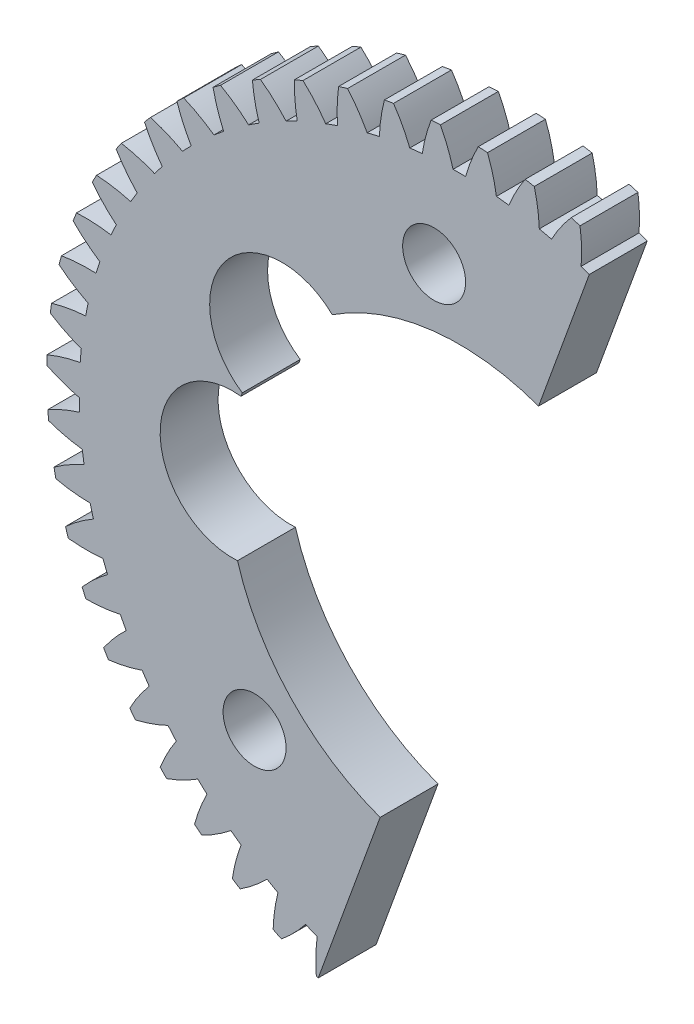
SolidWorks part; units mm, degrees
ref_plane "Front Plane" through (0, 0, 0) normal (0, 0, 1) x (1, 0, 0)
ref_plane "Top Plane" through (0, 0, 0) normal (0, 1, 0) x (1, 0, 0)
ref_plane "Right Plane" through (0, 0, 0) normal (1, 0, 0) x (0, 0, -1)
sketch "Model" plane through (0, 0, 0) normal (0, 0, 1) x (1, 0, 0)
  circle A0 centre (0, 0) radius 2.5
  arc A1 (-28.4774, 1.1339) -> (-28.4957, 0.4937) centre (0, 0) ccw
  arc A2 (-26.1862, 1.814) -> (-28.4774, 1.1339) centre (-24.2203, -9.0089) ccw
  arc A3 (-26.112, 2.6779) -> (-26.1862, 1.814) centre (0, 0) ccw
  arc A4 (-28.2537, 3.7387) -> (-26.112, 2.6779) centre (-22.3294, 13.0071) ccw
  arc A5 (-28.1626, 4.3727) -> (-28.2537, 3.7387) centre (0, 0) ccw
  arc A6 (-25.8088, 4.7871) -> (-28.1626, 4.3727) centre (-25.0894, -6.1893) ccw
  arc A7 (-25.6366, 5.637) -> (-25.8088, 4.7871) centre (0, 0) ccw
  arc A8 (-27.6434, 6.9351) -> (-25.6366, 5.637) centre (-20.7011, 15.4677) ccw
  arc A9 (-27.4805, 7.5545) -> (-27.6434, 6.9351) centre (0, 0) ccw
  arc A10 (-25.0949, 7.6979) -> (-27.4805, 7.5545) centre (-25.6314, -3.289) ccw
  arc A11 (-24.8269, 8.5226) -> (-25.0949, 7.6979) centre (0, 0) ccw
  arc A12 (-26.6726, 10.041) -> (-24.8269, 8.5226) centre (-18.803, 17.7266) ccw
  arc A13 (-26.4403, 10.6378) -> (-26.6726, 10.041) centre (0, 0) ccw
  arc A14 (-24.0538, 10.5083) -> (-26.4403, 10.6378) centre (-25.8392, -0.3458) ccw
  arc A15 (-23.6936, 11.2971) -> (-24.0538, 10.5083) centre (0, 0) ccw
  arc A16 (-25.3542, 13.016) -> (-23.6936, 11.2971) centre (-16.6598, 19.7544) ccw
  arc A17 (-25.0553, 13.5824) -> (-25.3542, 13.016) centre (0, 0) ccw
  arc A18 (-22.6991, 13.1818) -> (-25.0553, 13.5824) centre (-25.7102, 2.6019) ccw
  arc A19 (-22.2513, 13.9244) -> (-22.6991, 13.1818) centre (0, 0) ccw
  arc A20 (-23.7052, 15.8213) -> (-22.2513, 13.9244) centre (-14.2993, 21.5247) ccw
  arc A21 (-23.3437, 16.35) -> (-23.7052, 15.8213) centre (0, 0) ccw
  arc A22 (-21.0486, 15.6834) -> (-23.3437, 16.35) centre (-25.246, 5.5157) ccw
  arc A23 (-20.519, 16.3701) -> (-21.0486, 15.6834) centre (0, 0) ccw
  arc A24 (-21.7472, 18.4203) -> (-20.519, 16.3701) centre (-11.7525, 23.0144) ccw
  arc A25 (-21.3278, 18.9044) -> (-21.7472, 18.4203) centre (0, 0) ccw
  arc A26 (-19.1236, 17.9805) -> (-21.3278, 18.9044) centre (-24.4527, 8.3576) ccw
  arc A27 (-18.5192, 18.6024) -> (-19.1236, 17.9805) centre (0, 0) ccw
  arc A28 (-19.5057, 20.7793) -> (-18.5192, 18.6024) centre (-9.0524, 24.2041) ccw
  arc A29 (-19.0338, 21.2123) -> (-19.5057, 20.7793) centre (0, 0) ccw
  arc A30 (-16.9493, 20.0432) -> (-19.0338, 21.2123) centre (-23.3407, 11.0905) ccw
  arc A31 (-16.278, 20.5921) -> (-16.9493, 20.0432) centre (0, 0) ccw
  arc A32 (-17.0099, 22.8673) -> (-16.278, 20.5921) centre (-6.2344, 25.0782) ccw
  arc A33 (-16.4918, 23.2438) -> (-17.0099, 22.8673) centre (0, 0) ccw
  arc A34 (-14.5541, 21.8446) -> (-16.4918, 23.2438) centre (-21.9243, 13.6788) ccw
  arc A35 (-13.8246, 22.3135) -> (-14.5541, 21.8446) centre (0, 0) ccw
  arc A36 (-14.2923, 24.6572) -> (-13.8246, 22.3135) centre (-3.335, 25.6254) ccw
  arc A37 (-13.7347, 24.9722) -> (-14.2923, 24.6572) centre (0, 0) ccw
  arc A38 (-11.9691, 23.3613) -> (-13.7347, 24.9722) centre (-20.2221, 16.0889) ccw
  arc A39 (-11.1909, 23.7439) -> (-11.9691, 23.3613) centre (0, 0) ccw
  arc A40 (-11.3885, 26.1257) -> (-11.1909, 23.7439) centre (-0.3922, 25.8386) ccw
  arc A41 (-10.7985, 26.375) -> (-11.3885, 26.1257) centre (0, 0) ccw
  arc A42 (-9.2281, 24.5734) -> (-10.7985, 26.375) centre (-18.2563, 18.2891) ccw
  arc A43 (-8.4114, 24.8648) -> (-9.2281, 24.5734) centre (0, 0) ccw
  arc A44 (-8.3361, 27.2536) -> (-8.4114, 24.8648) centre (2.5557, 25.7149) ccw
  arc A45 (-7.7216, 27.434) -> (-8.3361, 27.2536) centre (0, 0) ccw
  arc A46 (-6.3668, 25.4651) -> (-7.7216, 27.434) centre (-16.0525, 20.251) ccw
  arc A47 (-5.5222, 25.6616) -> (-6.3668, 25.4651) centre (0, 0) ccw
  arc A48 (-5.1751, 28.0262) -> (-5.5222, 25.6616) centre (5.4703, 25.2559) ccw
  arc A49 (-4.544, 28.1354) -> (-5.1751, 28.0262) centre (0, 0) ccw
  arc A50 (-3.4225, 26.0249) -> (-4.544, 28.1354) centre (-13.6394, 21.9488) ccw
  arc A51 (-2.561, 26.1238) -> (-3.4225, 26.0249) centre (0, 0) ccw
  arc A52 (-1.9466, 28.4334) -> (-2.561, 26.1238) centre (8.3136, 24.4677) ccw
  arc A53 (-1.3072, 28.47) -> (-1.9466, 28.4334) centre (0, 0) ccw
  arc A54 (-0.4336, 26.2454) -> (-1.3072, 28.47) centre (-11.0486, 23.3605) ccw
  arc A55 (0.4336, 26.2454) -> (-0.4336, 26.2454) centre (0, 0) ccw
  arc A56 (1.3072, 28.47) -> (0.4336, 26.2454) centre (11.0486, 23.3605) ccw
  arc A57 (1.9466, 28.4334) -> (1.3072, 28.47) centre (0, 0) ccw
  arc A58 (2.561, 26.1238) -> (1.9466, 28.4334) centre (-8.3136, 24.4677) ccw
  arc A59 (3.4225, 26.0249) -> (2.561, 26.1238) centre (0, 0) ccw
  arc A60 (4.544, 28.1354) -> (3.4225, 26.0249) centre (13.6394, 21.9488) ccw
  arc A61 (5.1751, 28.0262) -> (4.544, 28.1354) centre (0, 0) ccw
  arc A62 (5.5222, 25.6616) -> (5.1751, 28.0262) centre (-5.4703, 25.2559) ccw
  arc A63 (6.3668, 25.4651) -> (5.5222, 25.6616) centre (0, 0) ccw
  arc A64 (7.7216, 27.434) -> (6.3668, 25.4651) centre (16.0525, 20.251) ccw
  arc A65 (8.3361, 27.2536) -> (7.7216, 27.434) centre (0, 0) ccw
  arc A66 (8.4114, 24.8648) -> (8.3361, 27.2536) centre (-2.5557, 25.7149) ccw
  arc A67 (9.2281, 24.5734) -> (8.4114, 24.8648) centre (0, 0) ccw
  arc A68 (10.7985, 26.375) -> (9.2281, 24.5734) centre (18.2563, 18.2891) ccw
  arc A69 (11.3885, 26.1257) -> (10.7985, 26.375) centre (0, 0) ccw
  arc A70 (11.1909, 23.7439) -> (11.3885, 26.1257) centre (0.3922, 25.8386) ccw
  arc A71 (11.9691, 23.3613) -> (11.1909, 23.7439) centre (0, 0) ccw
  arc A72 (13.7347, 24.9722) -> (11.9691, 23.3613) centre (20.2221, 16.0889) ccw
  arc A73 (14.2923, 24.6572) -> (13.7347, 24.9722) centre (0, 0) ccw
  arc A74 (13.8246, 22.3135) -> (14.2923, 24.6572) centre (3.335, 25.6254) ccw
  arc A75 (14.5541, 21.8446) -> (13.8246, 22.3135) centre (0, 0) ccw
  arc A76 (16.4918, 23.2438) -> (14.5541, 21.8446) centre (21.9243, 13.6788) ccw
  arc A77 (17.0099, 22.8673) -> (16.4918, 23.2438) centre (0, 0) ccw
  arc A78 (16.278, 20.5921) -> (17.0099, 22.8673) centre (6.2344, 25.0782) ccw
  arc A79 (16.9493, 20.0432) -> (16.278, 20.5921) centre (0, 0) ccw
  arc A80 (19.0338, 21.2123) -> (16.9493, 20.0432) centre (23.3407, 11.0905) ccw
  arc A81 (19.5057, 20.7793) -> (19.0338, 21.2123) centre (0, 0) ccw
  arc A82 (18.5192, 18.6024) -> (19.5057, 20.7793) centre (9.0524, 24.2041) ccw
  arc A83 (19.1236, 17.9805) -> (18.5192, 18.6024) centre (0, 0) ccw
  arc A84 (21.3278, 18.9044) -> (19.1236, 17.9805) centre (24.4527, 8.3576) ccw
  arc A85 (21.7472, 18.4203) -> (21.3278, 18.9044) centre (0, 0) ccw
  arc A86 (20.519, 16.3701) -> (21.7472, 18.4203) centre (11.7525, 23.0144) ccw
  arc A87 (21.0486, 15.6834) -> (20.519, 16.3701) centre (0, 0) ccw
  arc A88 (23.3437, 16.35) -> (21.0486, 15.6834) centre (25.246, 5.5157) ccw
  arc A89 (23.7052, 15.8213) -> (23.3437, 16.35) centre (0, 0) ccw
  arc A90 (22.2513, 13.9244) -> (23.7052, 15.8213) centre (14.2993, 21.5247) ccw
  arc A91 (22.6991, 13.1818) -> (22.2513, 13.9244) centre (0, 0) ccw
  arc A92 (25.0553, 13.5824) -> (22.6991, 13.1818) centre (25.7102, 2.6019) ccw
  arc A93 (25.3542, 13.016) -> (25.0553, 13.5824) centre (0, 0) ccw
  arc A94 (23.6936, 11.2971) -> (25.3542, 13.016) centre (16.6598, 19.7544) ccw
  arc A95 (24.0538, 10.5083) -> (23.6936, 11.2971) centre (0, 0) ccw
  arc A96 (26.4403, 10.6378) -> (24.0538, 10.5083) centre (25.8392, -0.3458) ccw
  arc A97 (26.6726, 10.041) -> (26.4403, 10.6378) centre (0, 0) ccw
  arc A98 (24.8269, 8.5226) -> (26.6726, 10.041) centre (18.803, 17.7266) ccw
  arc A99 (25.0949, 7.6979) -> (24.8269, 8.5226) centre (0, 0) ccw
  arc A100 (27.4805, 7.5545) -> (25.0949, 7.6979) centre (25.6314, -3.289) ccw
  arc A101 (27.6434, 6.9351) -> (27.4805, 7.5545) centre (0, 0) ccw
  arc A102 (25.6366, 5.637) -> (27.6434, 6.9351) centre (20.7011, 15.4677) ccw
  arc A103 (25.8088, 4.7871) -> (25.6366, 5.637) centre (0, 0) ccw
  arc A104 (28.1626, 4.3727) -> (25.8088, 4.7871) centre (25.0894, -6.1893) ccw
  arc A105 (28.2537, 3.7387) -> (28.1626, 4.3727) centre (0, 0) ccw
  arc A106 (26.112, 2.6779) -> (28.2537, 3.7387) centre (22.3294, 13.0071) ccw
  arc A107 (26.1862, 1.814) -> (26.112, 2.6779) centre (0, 0) ccw
  arc A108 (28.4774, 1.1339) -> (26.1862, 1.814) centre (24.2203, -9.0089) ccw
  arc A109 (28.4957, 0.4937) -> (28.4774, 1.1339) centre (0, 0) ccw
  arc A110 (26.2471, -0.3161) -> (28.4957, 0.4937) centre (23.6665, 10.377) ccw
  arc A111 (26.2223, -1.1829) -> (26.2471, -0.3161) centre (0, 0) ccw
  arc A112 (28.4211, -2.1197) -> (26.2223, -1.1829) centre (23.0355, -11.7111) ccw
  arc A113 (28.3663, -2.7578) -> (28.4211, -2.1197) centre (0, 0) ccw
  arc A114 (26.04, -3.3059) -> (28.3663, -2.7578) centre (24.6951, 7.6115) ccw
  arc A115 (25.9166, -4.1643) -> (26.04, -3.3059) centre (0, 0) ccw
  arc A116 (27.9942, -5.3456) -> (25.9166, -4.1643) centre (21.5504, -14.2606) ccw
  arc A117 (27.867, -5.9733) -> (27.9942, -5.3456) centre (0, 0) ccw
  arc A118 (25.4934, -6.2527) -> (27.867, -5.9733) centre (25.4018, 4.7469) ccw
  arc A119 (25.2729, -7.0914) -> (25.4934, -6.2527) centre (0, 0) ccw
  arc A120 (27.2024, -8.5019) -> (25.2729, -7.0914) centre (19.7843, -16.6242) ccw
  arc A121 (27.0044, -9.111) -> (27.2024, -8.5019) centre (0, 0) ccw
  arc A122 (24.6145, -9.118) -> (27.0044, -9.111) centre (25.7774, 1.8204) ccw
  arc A123 (24.2999, -9.9261) -> (24.6145, -9.118) centre (0, 0) ccw
  arc A124 (26.0559, -11.5473) -> (24.2999, -9.9261) centre (17.7604, -18.7711) ccw
  arc A125 (25.7898, -12.1299) -> (26.0559, -11.5473) centre (0, 0) ccw
  arc A126 (23.4147, -11.8644) -> (25.7898, -12.1299) centre (25.8168, -1.1299) ccw
  arc A127 (23.01, -12.6314) -> (23.4147, -11.8644) centre (0, 0) ccw
  arc A128 (24.5698, -14.4422) -> (23.01, -12.6314) centre (15.5048, -20.6733) ccw
  arc A129 (24.239, -14.9906) -> (24.5698, -14.4422) centre (0, 0) ccw
  arc A130 (21.9096, -14.4561) -> (24.239, -14.9906) centre (25.5198, -4.0654) ccw
  arc A131 (21.4201, -15.172) -> (21.9096, -14.4561) centre (0, 0) ccw
  arc A132 (22.7633, -17.1488) -> (21.4201, -15.172) centre (13.0472, -22.306) ccw
  arc A133 (22.3722, -17.656) -> (22.7633, -17.1488) centre (0, 0) ccw
  arc A134 (20.1189, -16.8594) -> (22.3722, -17.656) centre (24.89, -6.948) ccw
  arc A135 (19.551, -17.5148) -> (20.1189, -16.8594) centre (0, 0) ccw
  arc A136 (20.6601, -19.6318) -> (19.551, -17.5148) centre (10.4195, -23.6478) ccw
  arc A137 (20.2138, -20.0911) -> (20.6601, -19.6318) centre (0, 0) ccw
  arc A138 (18.0659, -19.0429) -> (20.2138, -20.0911) centre (23.9357, -9.7399) ccw
  arc A139 (17.4271, -19.6293) -> (18.0659, -19.0429) centre (0, 0) ccw
  arc A140 (18.2876, -21.8589) -> (17.4271, -19.6293) centre (7.6559, -24.6814) ccw
  arc A141 (17.7918, -22.2644) -> (18.2876, -21.8589) centre (0, 0) ccw
  arc A142 (15.7774, -20.9781) -> (17.7918, -22.2644) centre (22.6694, -12.4049) ccw
  arc A143 (15.0759, -21.4878) -> (15.7774, -20.9781) centre (0, 0) ccw
  arc A144 (15.6767, -23.8011) -> (15.0759, -21.4878) centre (4.7925, -25.3933) ccw
  arc A145 (15.1379, -24.1473) -> (15.6767, -23.8011) centre (0, 0) ccw
  arc A146 (13.2833, -22.6399) -> (15.1379, -24.1473) centre (21.1076, -14.9082) ccw
  arc A147 (12.5282, -23.0663) -> (13.2833, -22.6399) centre (0, 0) ccw
  arc A148 (12.8614, -25.433) -> (12.5282, -23.0663) centre (1.8667, -25.774) ccw
  arc A149 (12.2866, -25.7155) -> (12.8614, -25.433) centre (0, 0) ccw
  arc A150 (10.6159, -24.0065) -> (12.2866, -25.7155) centre (19.2706, -17.2171) ccw
  arc A151 (9.8172, -24.3441) -> (10.6159, -24.0065) centre (0, 0) ccw
  arc A152 (9.8784, -26.7333) -> (9.8172, -24.3441) centre (-1.0835, -25.8188) ccw
  arc A153 (9.2752, -26.9485) -> (9.8784, -26.7333) centre (0, 0) ccw
  arc A154 (7.8102, -25.0601) -> (9.2752, -26.9485) centre (17.1824, -19.3015) ccw
  arc A155 (6.9782, -25.3044) -> (7.8102, -25.0601) centre (0, 0) ccw
  arc A156 (6.7667, -27.6851) -> (6.9782, -25.3044) centre (-4.0196, -25.527) ccw
  arc A157 (6.1428, -27.8301) -> (6.7667, -27.6851) centre (0, 0) ccw
  arc A158 (4.9027, -25.7871) -> (6.1428, -27.8301) centre (14.8702, -21.1344) ccw
  arc A159 (4.0482, -25.935) -> (4.9027, -25.7871) centre (0, 0) ccw
  arc A160 (3.5667, -28.2759) -> (4.0482, -25.935) centre (-6.9032, -24.9024) ccw
  arc A161 (2.9304, -28.3489) -> (3.5667, -28.2759) centre (0, 0) ccw
  arc A162 (1.9312, -26.1779) -> (2.9304, -28.3489) centre (12.3642, -22.6917) ccw
  arc A163 (1.0654, -26.2274) -> (1.9312, -26.1779) centre (0, 0) ccw
  arc A164 (0.3202, -28.4982) -> (1.0654, -26.2274) centre (-9.6969, -23.9532) ccw
  arc A165 (-0.3202, -28.4982) -> (0.3202, -28.4982) centre (0, 0) ccw
  arc A166 (-1.0654, -26.2274) -> (-0.3202, -28.4982) centre (9.6969, -23.9532) ccw
  arc A167 (-1.9312, -26.1779) -> (-1.0654, -26.2274) centre (0, 0) ccw
  arc A168 (-2.9304, -28.3489) -> (-1.9312, -26.1779) centre (-12.3642, -22.6917) ccw
  arc A169 (-3.5667, -28.2759) -> (-2.9304, -28.3489) centre (0, 0) ccw
  arc A170 (-4.0482, -25.935) -> (-3.5667, -28.2759) centre (6.9032, -24.9024) ccw
  arc A171 (-4.9027, -25.7871) -> (-4.0482, -25.935) centre (0, 0) ccw
  arc A172 (-6.1428, -27.8301) -> (-4.9027, -25.7871) centre (-14.8702, -21.1344) ccw
  arc A173 (-6.7667, -27.6851) -> (-6.1428, -27.8301) centre (0, 0) ccw
  arc A174 (-6.9782, -25.3044) -> (-6.7667, -27.6851) centre (4.0196, -25.527) ccw
  arc A175 (-7.8102, -25.0601) -> (-6.9782, -25.3044) centre (0, 0) ccw
  arc A176 (-9.2752, -26.9485) -> (-7.8102, -25.0601) centre (-17.1824, -19.3015) ccw
  arc A177 (-9.8784, -26.7333) -> (-9.2752, -26.9485) centre (0, 0) ccw
  arc A178 (-9.8172, -24.3441) -> (-9.8784, -26.7333) centre (1.0835, -25.8188) ccw
  arc A179 (-10.6159, -24.0065) -> (-9.8172, -24.3441) centre (0, 0) ccw
  arc A180 (-12.2866, -25.7155) -> (-10.6159, -24.0065) centre (-19.2706, -17.2171) ccw
  arc A181 (-12.8614, -25.433) -> (-12.2866, -25.7155) centre (0, 0) ccw
  arc A182 (-12.5282, -23.0663) -> (-12.8614, -25.433) centre (-1.8667, -25.774) ccw
  arc A183 (-13.2833, -22.6399) -> (-12.5282, -23.0663) centre (0, 0) ccw
  arc A184 (-15.1379, -24.1473) -> (-13.2833, -22.6399) centre (-21.1076, -14.9082) ccw
  arc A185 (-15.6767, -23.8011) -> (-15.1379, -24.1473) centre (0, 0) ccw
  arc A186 (-15.0759, -21.4878) -> (-15.6767, -23.8011) centre (-4.7925, -25.3933) ccw
  arc A187 (-15.7774, -20.9781) -> (-15.0759, -21.4878) centre (0, 0) ccw
  arc A188 (-17.7918, -22.2644) -> (-15.7774, -20.9781) centre (-22.6694, -12.4049) ccw
  arc A189 (-18.2876, -21.8589) -> (-17.7918, -22.2644) centre (0, 0) ccw
  arc A190 (-17.4271, -19.6293) -> (-18.2876, -21.8589) centre (-7.6559, -24.6814) ccw
  arc A191 (-18.0659, -19.0429) -> (-17.4271, -19.6293) centre (0, 0) ccw
  arc A192 (-20.2138, -20.0911) -> (-18.0659, -19.0429) centre (-23.9357, -9.7399) ccw
  arc A193 (-20.6601, -19.6318) -> (-20.2138, -20.0911) centre (0, 0) ccw
  arc A194 (-19.551, -17.5148) -> (-20.6601, -19.6318) centre (-10.4195, -23.6478) ccw
  arc A195 (-20.1189, -16.8594) -> (-19.551, -17.5148) centre (0, 0) ccw
  arc A196 (-22.3722, -17.656) -> (-20.1189, -16.8594) centre (-24.89, -6.948) ccw
  arc A197 (-22.7633, -17.1488) -> (-22.3722, -17.656) centre (0, 0) ccw
  arc A198 (-21.4201, -15.172) -> (-22.7633, -17.1488) centre (-13.0472, -22.306) ccw
  arc A199 (-21.9096, -14.4561) -> (-21.4201, -15.172) centre (0, 0) ccw
  arc A200 (-24.239, -14.9906) -> (-21.9096, -14.4561) centre (-25.5198, -4.0654) ccw
  arc A201 (-24.5698, -14.4422) -> (-24.239, -14.9906) centre (0, 0) ccw
  arc A202 (-23.01, -12.6314) -> (-24.5698, -14.4422) centre (-15.5048, -20.6733) ccw
  arc A203 (-23.4147, -11.8644) -> (-23.01, -12.6314) centre (0, 0) ccw
  arc A204 (-25.7898, -12.1299) -> (-23.4147, -11.8644) centre (-25.8168, -1.1299) ccw
  arc A205 (-26.0559, -11.5473) -> (-25.7898, -12.1299) centre (0, 0) ccw
  arc A206 (-24.2999, -9.9261) -> (-26.0559, -11.5473) centre (-17.7604, -18.7711) ccw
  arc A207 (-24.6145, -9.118) -> (-24.2999, -9.9261) centre (0, 0) ccw
  arc A208 (-27.0044, -9.111) -> (-24.6145, -9.118) centre (-25.7774, 1.8204) ccw
  arc A209 (-27.2024, -8.5019) -> (-27.0044, -9.111) centre (0, 0) ccw
  arc A210 (-25.2729, -7.0914) -> (-27.2024, -8.5019) centre (-19.7843, -16.6242) ccw
  arc A211 (-25.4934, -6.2527) -> (-25.2729, -7.0914) centre (0, 0) ccw
  arc A212 (-27.867, -5.9733) -> (-25.4934, -6.2527) centre (-25.4018, 4.7469) ccw
  arc A213 (-27.9942, -5.3456) -> (-27.867, -5.9733) centre (0, 0) ccw
  arc A214 (-25.9166, -4.1643) -> (-27.9942, -5.3456) centre (-21.5504, -14.2606) ccw
  arc A215 (-26.04, -3.3059) -> (-25.9166, -4.1643) centre (0, 0) ccw
  arc A216 (-28.3663, -2.7578) -> (-26.04, -3.3059) centre (-24.6951, 7.6115) ccw
  arc A217 (-28.4211, -2.1197) -> (-28.3663, -2.7578) centre (0, 0) ccw
  arc A218 (-26.2223, -1.1829) -> (-28.4211, -2.1197) centre (-23.0355, -11.7111) ccw
  arc A219 (-26.2471, -0.3161) -> (-26.2223, -1.1829) centre (0, 0) ccw
  arc A220 (-28.4957, 0.4937) -> (-26.2471, -0.3161) centre (-23.6665, 10.377) ccw
extrude "Boss-Extrude1" add sketch "Model" along normal blind 4
sketch "Sketch2" plane through (0, 0, 4) normal (0, 0, 1) x (1, 0, 0)
  circle A0 centre (0, 0) radius 27.5 construction
  dimension "D1" = 55
sketch "Sketch3" plane through (0, 0, 4) normal (0, 0, 1) x (1, 0, 0)
  circle A0 centre (0, 0) radius 16
  dimension "D1" = 32
extrude "Cut-Extrude1" cut sketch "Sketch3" against normal blind 4
sketch "Sketch4" plane through (0, 0, 4) normal (0, 0, 1) x (1, 0, 0)
  line L0 (0, 0) -> (-16, 0) construction
  line L1 (0, 0) -> (-14.1421, -14.1421) construction
  circle A2 centre (0, 0) radius 16 construction
  circle A3 centre (-14.1421, -14.1421) radius 2.175
  dimension "D2" = 20
  dimension "D1" = 4.35
  dimension "D3" = 45
extrude "Cut-Extrude4" cut sketch "Sketch4" against normal blind 4
sketch "Sketch6" plane through (0, 0, 4) normal (0, 0, 1) x (1, 0, 0)
  line L0 (0, 0) -> (27.5, 0) construction
  line L1 (0, 0) -> (41.5501, -15.123)
  line L2 (0, 0) -> (13.5419, 37.2061)
  line L3 (13.5419, 37.2061) -> (41.5501, -15.123)
  line L4 (0, 0) -> (-13.5419, -37.2061)
  line L5 (-13.5419, -37.2061) -> (41.5501, -15.123)
  circle A0 centre (0, 0) radius 27.5 construction
  dimension "D1" = 20
  dimension "D2" = 90
extrude "Cut-Extrude5" cut sketch "Sketch6" against normal blind 4
sketch "Sketch7" plane through (0, 0, 4) normal (0, 0, 1) x (1, 0, 0)
  line L0 (0, 0) -> (-16, 0) construction
  line L1 (0, 0) -> (-13.9544, 5.079) construction
  line L2 (-12.2443, 9.7775) -> (-15.6645, 0.3805) construction
  arc A0 (5.4723, 15.0351) -> (-5.4723, -15.0351) centre (0, 0) ccw construction
  circle A1 centre (-12.2443, 9.7775) radius 5
  circle A2 centre (-15.6645, 0.3805) radius 5
  point P11 (-13.9544, 5.079)
  dimension "D1" = 10
  dimension "D2" = 10
  dimension "D3" = 14.85
  dimension "D4" = 20
extrude "Cut-Extrude6" cut sketch "Sketch7" against normal blind 4
pattern_circular "CirPattern2" count 2 over 130 about axis through (0, 0, 4) along (0, 0, 1) of "Cut-Extrude4"
